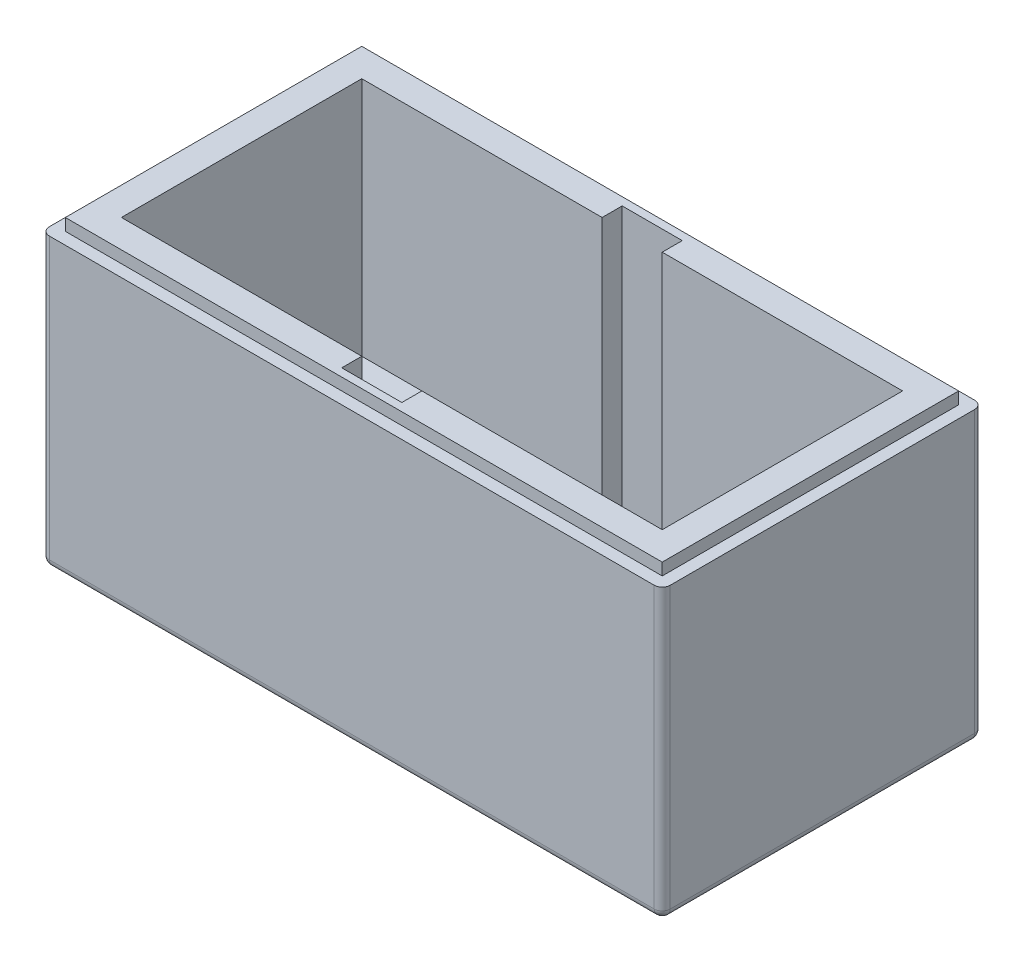
SolidWorks part; units mm, degrees
material "PVC 0.007 Plasticized"
ref_plane "Front Plane" through (0, 0, 0) normal (0, 0, 1) x (1, 0, 0)
ref_plane "Top Plane" through (0, 0, 0) normal (0, 1, 0) x (1, 0, 0)
ref_plane "Right Plane" through (0, 0, 0) normal (1, 0, 0) x (0, 0, -1)
sketch "Sketch2" plane through (0, 0, 0) normal (0, 1, 0) x (1, 0, 0)
  line L1 (0, 0) -> (-155, 0)
  line L2 (0, 0) -> (0, -80)
  line L3 (0, -80) -> (-155, -80)
  line L4 (-155, 0) -> (-155, -80)
  dimension "D1" = 155
  dimension "D2" = 80
extrude "Boss-Extrude1" add sketch "Sketch2" along normal blind 15
ref_plane "Plane1" through (0, 15, 0) normal (0, 1, 0) x (1, 0, 0)
sketch "Sketch3" plane through (0, 15, 0) normal (0, 1, 0) x (1, 0, 0)
  line L8 (-155, 0) -> (-155, -80) construction
  line L9 (-85, -5) -> (-70, -5)
  line L10 (-85, -5) -> (-85, -75)
  line L11 (-85, -75) -> (-70, -75)
  line L12 (-70, -5) -> (-70, -75)
  line L13 (0, -80) -> (0, 0) construction
  line L14 (0, 0) -> (-155, 0) construction
  line L15 (-155, -80) -> (0, -80) construction
  point P10 (-77.5, 0)
  point P13 (-77.5, -80)
  dimension "D1" = 70
  dimension "D2" = 70
  dimension "D3" = 15
  dimension "D4" = 5
  dimension "D5" = 5
  dimension "D6" = 70
extrude "Cut-Extrude1" cut sketch "Sketch3" against normal blind 5
sketch "Sketch4" plane through (0, 15, 0) normal (0, 1, 0) x (1, 0, 0)
  line L0 (-145, -10) -> (-145, -70)
  line L1 (-155, 0) -> (0, 0)
  line L2 (-155, 0) -> (-155, -80)
  line L3 (-155, -80) -> (0, -80)
  line L4 (0, 0) -> (0, -80)
  line L5 (-145, -70) -> (-85, -70)
  line L6 (-85, -5) -> (-85, -75) construction
  line L7 (-145, -10) -> (-85, -10)
  line L8 (-85, -10) -> (-85, -5)
  line L9 (-85, -5) -> (-70, -5)
  line L10 (-70, -5) -> (-70, -10)
  line L11 (-70, -75) -> (-70, -5) construction
  line L12 (-70, -10) -> (-10, -10)
  line L13 (-10, -10) -> (-10, -70)
  line L14 (-10, -70) -> (-70, -70)
  line L15 (-70, -70) -> (-70, -75)
  line L16 (-85, -70) -> (-85, -75)
  line L17 (-85, -75) -> (-70, -75)
  dimension "D1" = 10
  dimension "D2" = 10
  dimension "D3" = 10
  dimension "D4" = 10
  dimension "D5" = 10
  dimension "D6" = 10
  dimension "D7" = 60
  dimension "D8" = 60
  dimension "D9" = 15
  dimension "D10" = 60
  dimension "D11" = 60
extrude "Boss-Extrude3" add sketch "Sketch4" along normal blind 60
ref_plane "Plane2" through (0, 75, 0) normal (0, 1, 0) x (1, 0, 0)
sketch "Sketch5" plane through (0, 75, 0) normal (0, 1, 0) x (1, 0, 0)
  line L1 (-155, 0) -> (0, 0)
  line L2 (-155, 0) -> (-155, -80)
  line L3 (-155, -80) -> (0, -80)
  line L4 (0, 0) -> (0, -80)
  line L5 (-152, -3) -> (-3, -3)
  line L6 (-152, -3) -> (-152, -77)
  line L7 (-152, -77) -> (-3, -77)
  line L8 (-3, -3) -> (-3, -77)
  dimension "D1" = 3
  dimension "D2" = 3
  dimension "D3" = 3
  dimension "D4" = 3
extrude "Cut-Extrude2" cut sketch "Sketch5" against normal blind 3
fillet "Fillet1" radius 2 8 edges at (-77.5, 0, 80) (0, 36, 80) (0, 0, 40) (0, 36, 0) (-77.5, 0, 0) (-155, 0, 40) (-155, 36, 0) (-155, 36, 80)
